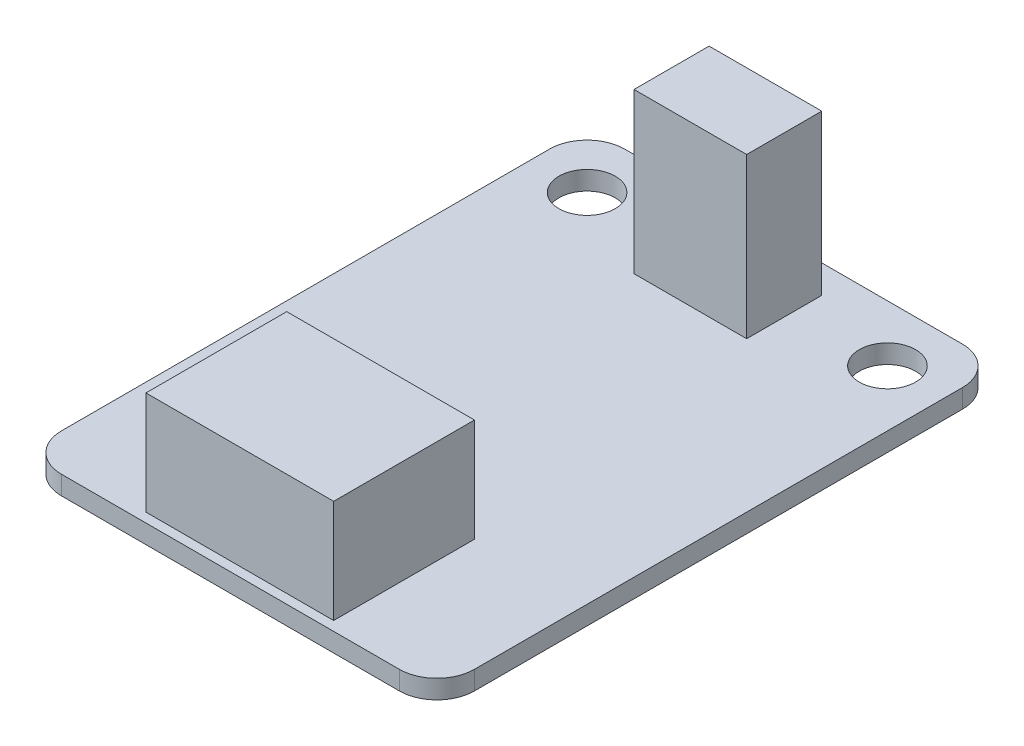
SolidWorks part; units mm, degrees
ref_plane "Plan de face" through (0, 0, 0) normal (0, 0, 1) x (1, 0, 0)
ref_plane "Plan de dessus" through (0, 0, 0) normal (0, 1, 0) x (1, 0, 0)
ref_plane "Plan de droite" through (0, 0, 0) normal (1, 0, 0) x (0, 0, -1)
sketch "Esquisse1" plane through (0, 0, 0) normal (0, 1, 0) x (1, 0, 0)
  line L1 (2, 0) -> (20, 0)
  line L2 (0, 2) -> (0, 28)
  line L3 (2, 30) -> (20, 30)
  line L4 (22, 2) -> (22, 28)
  arc A0 (2, 0) -> (0, 2) centre (2, 2) cw
  arc A1 (20, 0) -> (22, 2) centre (20, 2) ccw
  arc A2 (20, 30) -> (22, 28) centre (20, 28) cw
  arc A3 (0, 28) -> (2, 30) centre (2, 28) cw
  point P7 (0, 0)
  point P12 (22, 30)
  point P15 (0, 30)
  dimension "D3" = 2
  dimension "D1" = 22
  dimension "D2" = 30
extrude "Boss.-Extru.1" add sketch "Esquisse1" along normal blind 1
sketch "Esquisse3" plane through (0, 1, 0) normal (0, 1, 0) x (1, 0, 0)
  line L1 (20, 30) -> (2, 30) construction
  line L2 (0, 28) -> (0, 2) construction
  line L3 (22, 2) -> (22, 28) construction
  circle A0 centre (3, 27) radius 1.5
  circle A1 centre (19, 27) radius 1.5
  dimension "D1" = 3
  dimension "D2" = 3
  dimension "D3" = 3
  dimension "D4" = 3
  dimension "D5" = 3
extrude "Enlèv. mat.-Extru.1" cut sketch "Esquisse3" against normal up to surface (1 mm away) up to face at (11, 0, -15)
sketch "Esquisse4" plane through (0, 1, 0) normal (0, 1, 0) x (1, 0, 0)
  line L0 (20, 30) -> (2, 30) construction
  line L1 (8, 28.5) -> (14, 28.5)
  line L2 (8, 28.5) -> (8, 24.5)
  line L3 (8, 24.5) -> (14, 24.5)
  line L4 (14, 28.5) -> (14, 24.5)
  line L5 (0, 28) -> (0, 2) construction
  dimension "D1" = 6
  dimension "D2" = 4
  dimension "D3" = 1.5
  dimension "D4" = 8
extrude "Boss.-Extru.2" add sketch "Esquisse4" along normal blind 8.5
ref_plane "Plan1" through (11, 0, 0) normal (1, 0, 0) x (0, 0, -1)
sketch "Esquisse6" plane through (11, 0, 0) normal (1, 0, 0) x (0, 0, -1)
  line L0 (28.5, 6.5) -> (30, 6.5)
  line L1 (28.5, 9.5) -> (28.5, 1) construction
  line L2 (28.5, 4) -> (28.5, 6.5)
  line L3 (24.5, 9.5) -> (28.5, 9.5) construction
  arc A0 (30, 6.5) -> (28.5, 4) centre (27.1667, 6.5) cw
  dimension "D1" = 1.5
  dimension "D2" = 3
  dimension "D3" = 2.5
revolve "Révolution1" add sketch "Esquisse6" angle 360 about L0
sketch "Esquisse7" plane through (0, 1, 0) normal (0, 1, 0) x (1, 0, 0)
  line L0 (2, 0) -> (20, 0) construction
  line L1 (16, 8) -> (6, 8)
  line L2 (16, 8) -> (16, 0.5)
  line L3 (16, 0.5) -> (6, 0.5)
  line L4 (6, 8) -> (6, 0.5)
  line L5 (22, 2) -> (22, 28) construction
  dimension "D1" = 10
  dimension "D2" = 7.5
  dimension "D3" = 0.5
  dimension "D4" = 6
extrude "Boss.-Extru.4" add sketch "Esquisse7" along normal blind 5.5
